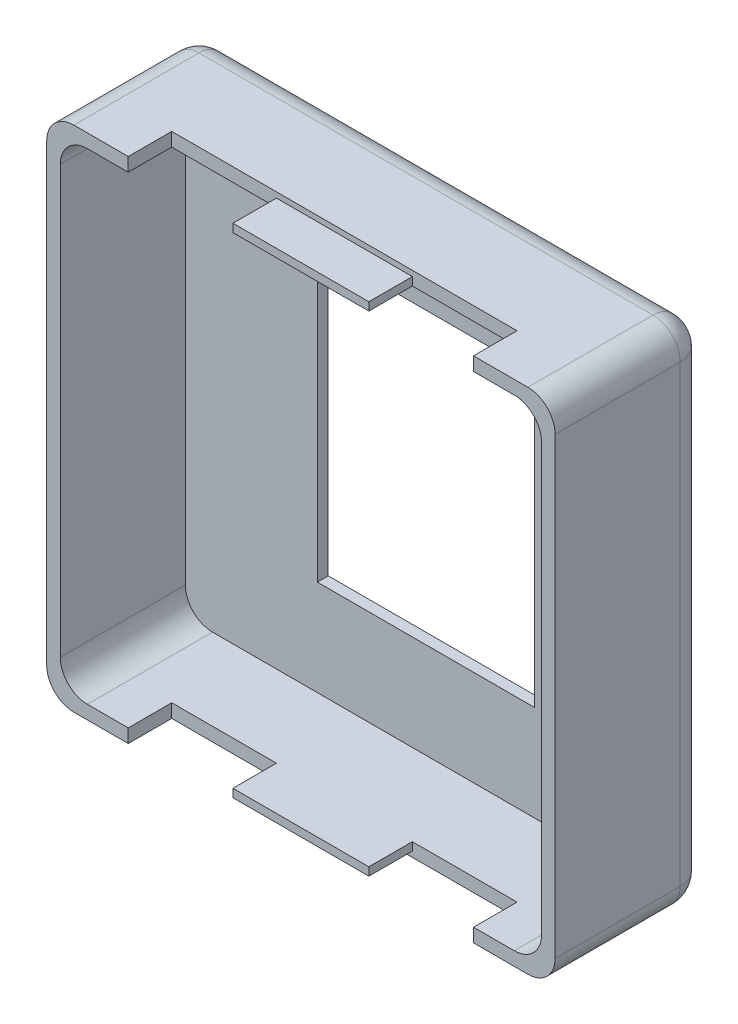
SolidWorks part; units mm, degrees
ref_plane "Front Plane" through (0, 0, 0) normal (0, 0, 1) x (1, 0, 0)
ref_plane "Top Plane" through (0, 0, 0) normal (0, 1, 0) x (1, 0, 0)
ref_plane "Right Plane" through (0, 0, 0) normal (1, 0, 0) x (0, 0, -1)
sketch "Sketch1" plane through (0, 0, 0) normal (0, 0, 1) x (1, 0, 0)
  line L1 (-21.209, -23.749) -> (21.209, -23.749)
  line L2 (-23.749, -21.209) -> (-23.749, 21.209)
  line L3 (-21.209, 23.749) -> (21.209, 23.749)
  line L4 (23.749, -21.209) -> (23.749, 21.209)
  line L5 (-23.749, -23.749) -> (23.749, 23.749) construction
  line L6 (-23.749, 23.749) -> (23.749, -23.749) construction
  arc A0 (-21.209, -23.749) -> (-23.749, -21.209) centre (-21.209, -21.209) cw
  arc A1 (21.209, -23.749) -> (23.749, -21.209) centre (21.209, -21.209) ccw
  arc A2 (21.209, 23.749) -> (23.749, 21.209) centre (21.209, 21.209) cw
  arc A3 (-23.749, 21.209) -> (-21.209, 23.749) centre (-21.209, 21.209) cw
  point P0 (0, 0)
  dimension "D3" = 2.54
  dimension "D1" = 47.498
  dimension "D2" = 47.498
extrude "Boss-Extrude1" add sketch "Sketch1" along normal blind 14.224
sketch "Sketch2" plane through (0, 0, 14.224) normal (0, 0, 1) x (1, 0, 0)
  line L22 (21.209, 23.749) -> (-21.209, 23.749) construction
  line L23 (19.939, -22.479) -> (-19.939, -22.479)
  line L24 (22.479, -19.939) -> (22.479, 19.939)
  line L25 (19.939, 22.479) -> (-19.939, 22.479)
  line L26 (-22.479, -19.939) -> (-22.479, 19.939)
  line L27 (22.479, -22.479) -> (-22.479, 22.479) construction
  line L28 (22.479, 22.479) -> (-22.479, -22.479) construction
  line L29 (-23.749, 21.209) -> (-23.749, -21.209) construction
  arc A14 (-19.939, -22.479) -> (-22.479, -19.939) centre (-19.939, -19.939) cw
  arc A15 (19.939, -22.479) -> (22.479, -19.939) centre (19.939, -19.939) ccw
  arc A16 (22.479, 19.939) -> (19.939, 22.479) centre (19.939, 19.939) ccw
  arc A17 (-19.939, 22.479) -> (-22.479, 19.939) centre (-19.939, 19.939) ccw
  point P12 (0, 0)
  dimension "D3" = 2.54
  dimension "D1" = 1.27
  dimension "D2" = 1.27
extrude "Cut-Extrude1" cut sketch "Sketch2" against normal blind 11.684
fillet "Fillet1" radius 2.54 8 edges at (-23.0051, 23.0051, 0) (0, 23.749, 0) (23.0051, 23.0051, 0) (23.749, 0, 0) (23.0051, -23.0051, 0) (0, -23.749, 0) (-23.0051, -23.0051, 0) (-23.749, 0, 0)
sketch "Sketch3" plane through (0, 23.749, 0) normal (0, 1, 0) x (1, 0, 0)
  line L0 (21.209, -14.224) -> (-21.209, -14.224) construction
  line L1 (16.129, -18.288) -> (-16.129, -18.288)
  line L2 (16.129, -18.288) -> (16.129, -10.16)
  line L3 (16.129, -10.16) -> (-16.129, -10.16)
  line L4 (-16.129, -18.288) -> (-16.129, -10.16)
  line L5 (16.129, -18.288) -> (-16.129, -10.16) construction
  line L6 (16.129, -10.16) -> (-16.129, -18.288) construction
  point P0 (0, -14.224)
  dimension "D1" = 32.258
  dimension "D2" = 4.064
extrude "Cut-Extrude2" cut sketch "Sketch3" against normal through all both and the other way through all
sketch "Sketch4" plane through (23.749, 0, 0) normal (1, 0, 0) x (0, 0, -1)
  line L0 (-14.224, -21.209) -> (-14.224, 21.209) construction
  circle A0 centre (-14.224, -14.986) radius 1.778
  point P4 (-14.224, 0)
  dimension "D2" = 3.556
  dimension "D1" = 14.986
sketch "Sketch5" plane through (0, 0, 0) normal (0, 0, -1) x (-1, 0, 0)
  line L1 (-13.462, 17.145) -> (13.462, 17.145)
  line L2 (-13.462, 17.145) -> (-13.462, -17.145)
  line L3 (-13.462, -17.145) -> (13.462, -17.145)
  line L4 (13.462, 17.145) -> (13.462, -17.145)
  line L5 (-13.462, 17.145) -> (13.462, -17.145) construction
  line L6 (-13.462, -17.145) -> (13.462, 17.145) construction
  point P0 (0, 0)
  dimension "D1" = 26.924
  dimension "D2" = 34.29
extrude "Cut-Extrude4" cut sketch "Sketch5" against normal blind 1.524
sketch "Sketch6" plane through (0, 0, 1.524) normal (0, 0, -1) x (-1, 0, 0)
  line L1 (-10.1453, -13.5361) -> (10.1453, -13.5361)
  line L2 (-10.1453, -13.5361) -> (-10.1453, 13.5361)
  line L3 (-10.1453, 13.5361) -> (10.1453, 13.5361)
  line L4 (10.1453, -13.5361) -> (10.1453, 13.5361)
  line L5 (-10.1453, -13.5361) -> (10.1453, 13.5361) construction
  line L6 (-10.1453, 13.5361) -> (10.1453, -13.5361) construction
  point P0 (0, 0)
extrude "Cut-Extrude5" cut sketch "Sketch6" against normal blind 1.524
sketch "Sketch7" plane through (0, 0, 0) normal (0, 0, -1) x (-1, 0, 0)
  line L0 (21.209, 21.209) -> (21.209, -21.209) construction
  line L1 (21.209, 21.209) -> (-21.209, 21.209) construction
  line L2 (-21.209, -21.209) -> (21.209, -21.209) construction
  line L3 (13.589, 21.209) -> (13.589, -21.209) construction
  line L4 (21.209, -21.209) -> (21.209, 21.209) construction
  line L5 (13.589, 17.145) -> (21.209, 17.145) construction
  line L6 (19.939, 17.145) -> (21.209, 17.145)
  line L7 (14.859, 17.145) -> (13.589, 17.145)
  line L8 (21.209, 15.875) -> (16.129, 15.875)
  line L9 (21.209, 10.795) -> (16.129, 10.795)
  line L10 (16.129, 14.605) -> (21.209, 14.605)
  line L11 (21.209, 14.605) -> (21.209, 15.875)
  line L12 (16.129, 12.065) -> (21.209, 12.065)
  line L13 (21.209, 12.065) -> (21.209, 10.795)
  line L14 (13.589, 9.525) -> (21.209, 9.525)
  line L15 (21.209, 9.525) -> (21.209, 5.715)
  line L16 (21.209, 5.715) -> (19.939, 5.715)
  line L17 (19.939, 5.715) -> (19.939, 8.255)
  line L18 (19.939, 8.255) -> (18.034, 8.255)
  line L19 (18.034, 8.255) -> (18.034, 6.985)
  line L20 (18.034, 6.985) -> (16.764, 6.985)
  line L21 (16.764, 6.985) -> (16.764, 8.255)
  line L22 (16.764, 8.255) -> (13.589, 8.255)
  line L23 (13.589, 8.255) -> (13.589, 9.525)
  line L24 (13.589, 4.445) -> (21.209, 4.445)
  line L25 (21.209, 4.445) -> (21.209, 0.635)
  line L26 (21.209, 0.635) -> (19.939, 0.635)
  line L27 (19.939, 0.635) -> (19.939, 3.175)
  line L28 (19.939, 3.175) -> (18.034, 3.175)
  line L29 (18.034, 3.175) -> (18.034, 1.905)
  line L30 (18.034, 1.905) -> (16.764, 1.905)
  line L31 (16.764, 1.905) -> (16.764, 3.175)
  line L32 (16.764, 3.175) -> (13.589, 3.175)
  line L33 (13.589, 3.175) -> (13.589, 4.445)
  line L34 (21.209, -0.635) -> (13.589, -0.635)
  line L35 (13.589, -0.635) -> (13.589, -4.445)
  line L36 (13.589, -4.445) -> (14.859, -4.445)
  line L37 (14.859, -4.445) -> (14.859, -1.905)
  line L38 (14.859, -1.905) -> (21.209, -1.905)
  line L39 (21.209, -1.905) -> (21.209, -0.635)
  line L40 (13.589, -5.715) -> (21.209, -5.715)
  line L41 (21.209, -5.715) -> (21.209, -9.525)
  line L42 (21.209, -9.525) -> (19.939, -9.525)
  line L43 (19.939, -9.525) -> (19.939, -6.985)
  line L44 (19.939, -6.985) -> (18.034, -6.985)
  line L45 (18.034, -6.985) -> (18.034, -8.255)
  line L46 (18.034, -8.255) -> (16.764, -8.255)
  line L47 (16.764, -8.255) -> (16.764, -6.985)
  line L48 (16.764, -6.985) -> (14.859, -6.985)
  line L49 (14.859, -6.985) -> (14.859, -9.525)
  line L50 (14.859, -9.525) -> (13.589, -9.525)
  line L51 (13.589, -9.525) -> (13.589, -5.715)
  line L52 (13.589, -13.0175) -> (21.209, -13.0175) construction
  line L53 (21.209, -13.0175) -> (17.399, -13.0175) construction
  line L54 (17.399, -13.0175) -> (13.589, -13.0175) construction
  line L55 (18.9865, -13.97) -> (18.9865, -15.24)
  line L56 (15.8115, -12.065) -> (15.8115, -10.795)
  line L57 (13.589, -18.7325) -> (21.209, -18.7325) construction
  line L58 (15.8115, -17.78) -> (15.8115, -16.51)
  line L59 (18.9865, -20.955) -> (18.9865, -19.685)
  arc A0 (21.209, 17.145) -> (13.589, 17.145) centre (17.399, 17.145) ccw
  arc A1 (19.939, 17.145) -> (14.859, 17.145) centre (17.399, 17.145) ccw
  arc A2 (16.129, 15.875) -> (16.129, 10.795) centre (16.129, 13.335) ccw
  arc A3 (16.129, 14.605) -> (16.129, 12.065) centre (16.129, 13.335) ccw
  arc A4 (18.9865, -15.24) -> (16.764, -13.0175) centre (18.9865, -13.0175) ccw
  arc A5 (15.8115, -10.795) -> (18.034, -13.0175) centre (15.8115, -13.0175) ccw
  arc A6 (18.9865, -13.97) -> (18.034, -13.0175) centre (18.9865, -13.0175) ccw
  arc A7 (15.8115, -12.065) -> (16.764, -13.0175) centre (15.8115, -13.0175) ccw
  arc A8 (15.8115, -16.51) -> (18.034, -18.7325) centre (15.8115, -18.7325) ccw
  arc A9 (18.9865, -20.955) -> (16.764, -18.7325) centre (18.9865, -18.7325) ccw
  arc A10 (15.8115, -17.78) -> (16.764, -18.7325) centre (15.8115, -18.7325) ccw
  arc A11 (18.9865, -19.685) -> (18.034, -18.7325) centre (18.9865, -18.7325) ccw
  point P15 (13.589, 0)
  dimension "D3" = 5.08
  dimension "D4" = 17.145
  dimension "D5" = 2.54
  dimension "D6" = 5.08
  dimension "D40" = 4.445
  dimension "D41" = 1.27
  dimension "D42" = 1.905
  dimension "D43" = 4.445
  dimension "D44" = 1.27
  dimension "D46" = 1.905
  dimension "D1" = 7.62
  dimension "D2" = 0
  dimension "D7" = 1.27
  dimension "D8" = 1.27
  dimension "D9" = 1.27
  dimension "D10" = 1.27
  dimension "D11" = 1.27
  dimension "D12" = 1.27
  dimension "D13" = 1.905
  dimension "D14" = 1.27
  dimension "D15" = 2.54
  dimension "D16" = 3.81
  dimension "D17" = 1.27
  dimension "D18" = 1.27
  dimension "D19" = 1.27
  dimension "D20" = 1.27
  dimension "D21" = 1.905
  dimension "D22" = 1.27
  dimension "D23" = 2.54
  dimension "D24" = 3.81
  dimension "D25" = 1.27
  dimension "D26" = 1.27
  dimension "D27" = 1.27
  dimension "D28" = 3.81
  dimension "D29" = 1.27
  dimension "D30" = 1.27
  dimension "D31" = 1.27
  dimension "D32" = 1.27
  dimension "D33" = 1.27
  dimension "D34" = 2.54
  dimension "D35" = 2.54
  dimension "D36" = 3.81
  dimension "D37" = 3.81
  dimension "D38" = 1.905
  dimension "D39" = 1.27
extrude "Boss-Extrude2" add sketch "Sketch7" along normal blind 0.762
sketch "Sketch8" plane through (0, 0, 10.16) normal (0, 0, 1) x (1, 0, 0)
  line L0 (16.129, 22.479) -> (-16.129, 22.479) construction
  line L1 (6.35, 23.241) -> (-6.35, 23.241)
  line L2 (6.35, 23.241) -> (6.35, 22.479)
  line L3 (6.35, 22.479) -> (-6.35, 22.479)
  line L4 (-6.35, 23.241) -> (-6.35, 22.479)
  line L5 (6.35, 23.241) -> (-6.35, 22.479) construction
  line L6 (6.35, 22.479) -> (-6.35, 23.241) construction
  line L7 (-16.129, -22.479) -> (16.129, -22.479) construction
  line L8 (6.35, -23.241) -> (-6.35, -23.241)
  line L9 (6.35, -23.241) -> (6.35, -22.479)
  line L10 (6.35, -22.479) -> (-6.35, -22.479)
  line L11 (-6.35, -23.241) -> (-6.35, -22.479)
  line L12 (6.35, -23.241) -> (-6.35, -22.479) construction
  line L13 (6.35, -22.479) -> (-6.35, -23.241) construction
  point P0 (0, 22.86)
  point P7 (0, -22.86)
  dimension "D1" = 0.762
  dimension "D2" = 12.7
  dimension "D3" = 0
  dimension "D4" = 0.762
  dimension "D5" = 12.7
  dimension "D6" = 0
extrude "Boss-Extrude3" add sketch "Sketch8" along normal blind 4.064
